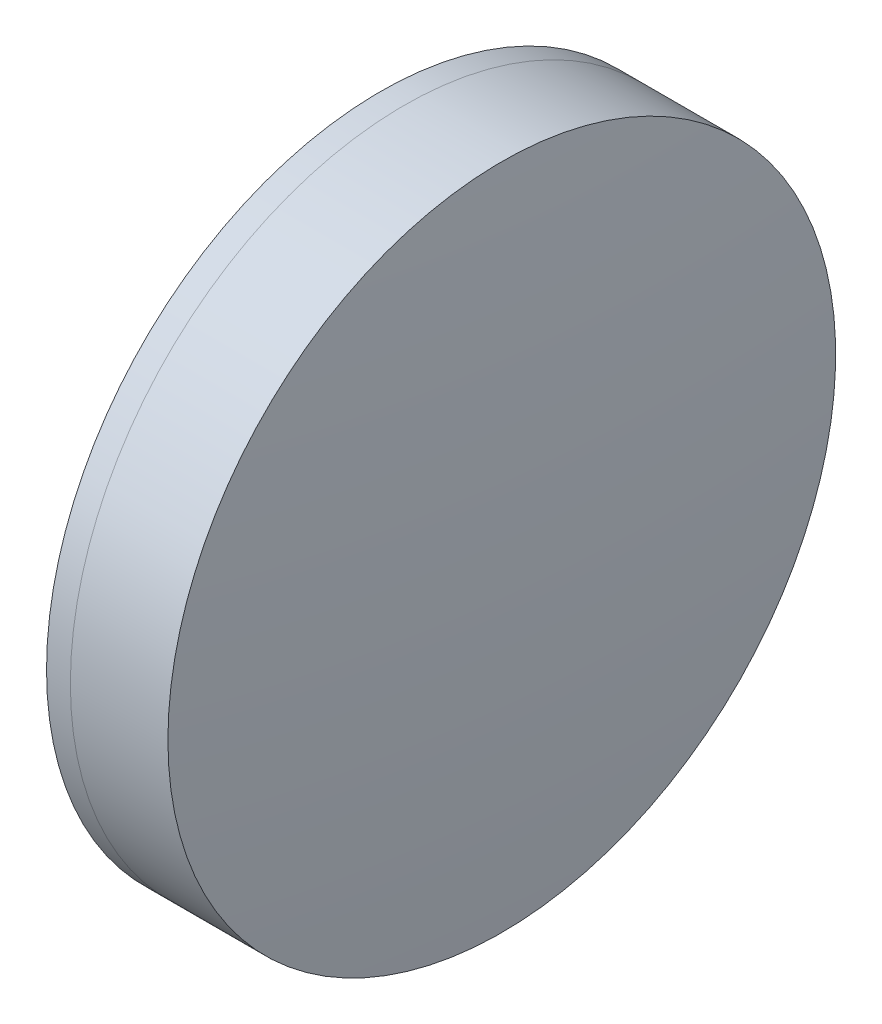
SolidWorks part; units mm, degrees
ref_plane "前视基准面" through (0, 0, 0) normal (0, 0, 1) x (1, 0, 0)
ref_plane "上视基准面" through (0, 0, 0) normal (0, 1, 0) x (1, 0, 0)
ref_plane "右视基准面" through (0, 0, 0) normal (1, 0, 0) x (0, 0, -1)
sketch "草图1" plane through (0, 0, 0) normal (0, 1, 0) x (1, 0, 0)
  line L0 (124.5233, 0) -> (646.9917, 0) construction
  line L1 (534.6417, -25.4) -> (536.4549, -25.4)
  line L2 (534.6417, 25.4) -> (536.4549, 25.4)
  arc A0 (536.4549, -25.4) -> (536.4549, 25.4) centre (446.8868, 0) ccw
  arc A1 (534.6417, 25.4) -> (534.6417, -25.4) centre (579.7868, 0) ccw
  point P10 (527.9868, 0)
  point P11 (539.9868, 0)
  dimension "D3" = 51.8
  dimension "D4" = 93.1
  dimension "D1" = 25.4
  dimension "D2" = 25.4
  dimension "D5" = 12
revolve "旋转1" add sketch "草图1" angle 360 about L0
sketch "草图2" plane through (0, 0, 0) normal (0, 1, 0) x (1, 0, 0)
  line L0 (-0.5519, 0) -> (622.6607, 0) construction
  line L2 (536.4549, 25.4) -> (543.8765, 25.4)
  line L3 (536.4549, -25.4) -> (543.8765, -25.4)
  arc A0 (543.8765, -25.4) -> (543.8765, 25.4) centre (253.8868, 0) ccw
  arc A1 (536.4549, -25.4) -> (536.4549, 25.4) centre (446.8868, 0) ccw construction
  arc A2 (536.4549, -25.4) -> (536.4549, 25.4) centre (446.8868, 0) ccw
  point P4 (539.9868, 0)
  point P8 (544.9868, 0)
  dimension "D1" = 291.1
  dimension "D2" = 5
revolve "旋转3" add sketch "草图2" angle 360 about L0
